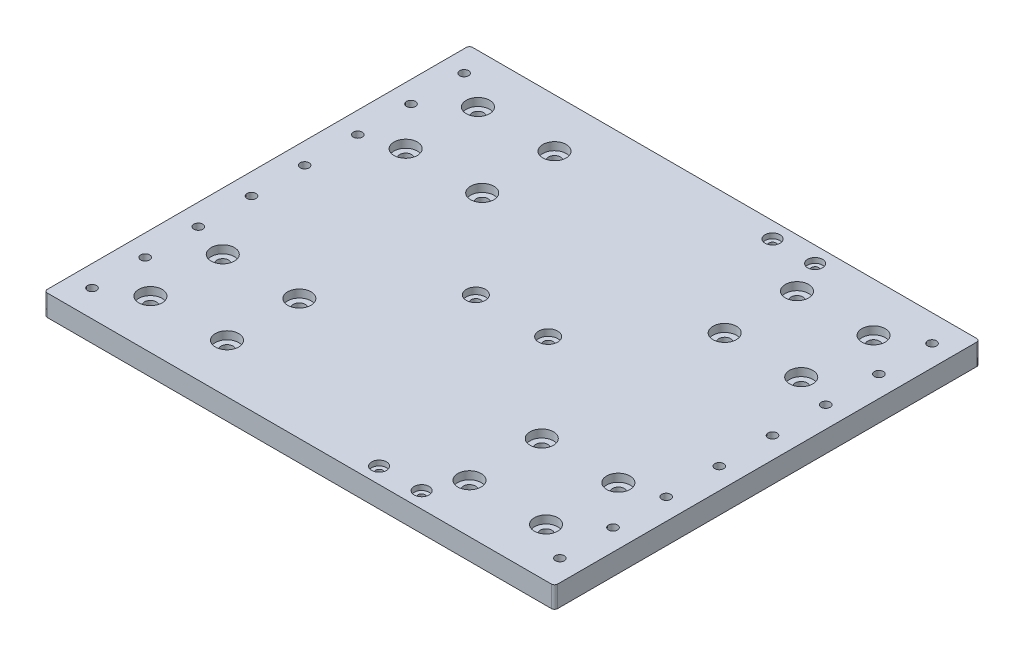
SolidWorks part; units mm, degrees
ref_plane "Front Plane" through (0, 0, 0) normal (0, 0, 1) x (1, 0, 0)
ref_plane "Top Plane" through (0, 0, 0) normal (0, 1, 0) x (1, 0, 0)
ref_plane "Right Plane" through (0, 0, 0) normal (1, 0, 0) x (0, 0, -1)
sketch "Sketch1" plane through (0, 0, 0) normal (0, 1, 0) x (1, 0, 0)
  line L1 (-120, -100) -> (120, -100)
  line L2 (-120, -100) -> (-120, 100)
  line L3 (-120, 100) -> (120, 100)
  line L4 (120, -100) -> (120, 100)
  line L5 (-120, -100) -> (120, 100) construction
  line L6 (-120, 100) -> (120, -100) construction
  point P0 (0, 0)
  dimension "D1" = 240
  dimension "D2" = 200
extrude "Boss-Extrude1" add sketch "Sketch1" along normal mid plane 10
hole_wizard "CBORE for M5 Pan Head Machine Screw1" positions "Sketch11" profile "Sketch10" counterbore size "M5" standard "ANSI Metric" end condition through all
sketch "Sketch11" plane through (66.9231, 5, -81.9693) normal (0, -1, 0) x (-1, 0, 0)
  line L0 (141.9231, -1018.8886) -> (141.9231, 48981.1114) construction
  line L1 (-912.3245, -141.9693) -> (49087.6755, -141.9693) construction
  line L2 (186.9231, 18.0307) -> (186.9231, -181.9693) construction
  line L3 (186.9231, -181.9693) -> (-53.0769, -181.9693) construction
  line L5 (159.9231, -124.9693) -> (123.9231, -124.9693) construction
  line L6 (159.9231, -124.9693) -> (159.9231, -158.9693) construction
  line L7 (159.9231, -158.9693) -> (123.9231, -158.9693) construction
  line L8 (123.9231, -124.9693) -> (123.9231, -158.9693) construction
  line L9 (159.9231, -124.9693) -> (123.9231, -158.9693) construction
  line L10 (159.9231, -158.9693) -> (123.9231, -124.9693) construction
  point P0 (159.9231, -158.9693)
  point P2 (123.9231, -158.9693)
  point P4 (123.9231, -124.9693)
  point P6 (159.9231, -124.9693)
  dimension "D1" = 45
  dimension "D2" = 40
  dimension "D3" = 18
  dimension "D4" = 34
  dimension "D5" = 17
  dimension "D6" = 36
sketch "Sketch10" plane through (-93, 5, 77) normal (1, 0, 0) x (0, 0, 1)
  line L0 (0, 0) -> (0, 10)
  line L1 (0, 10) -> (2.75, 10)
  line L3 (2.75, 10) -> (2.75, 3.7)
  line L4 (2.75, 3.7) -> (5.5, 3.7)
  line L5 (5.5, 3.7) -> (5.5, 0)
  line L7 (5.5, 0) -> (0, 0)
  line L11 (0, -6.35) -> (0, 107.95) construction
  dimension "Thru Hole Dia." = 5.5
  dimension "Thru Hole Depth" = 10
  dimension "C'Bore Dia." = 11
  dimension "C'Bore Depth" = 3.7
mirror "Mirror1" about plane through (0, 0, 0) normal (1, 0, 0) of "CBORE for M5 Pan Head Machine Screw1"
mirror "Mirror2" about plane through (0, 0, 0) normal (0, 0, 1) of "Mirror1", "CBORE for M5 Pan Head Machine Screw1"
hole_wizard "CBORE for M4 Pan Head Machine Screw1" positions "Sketch9" profile "Sketch8" counterbore size "M4" standard "ANSI Metric" end condition through all
sketch "Sketch9" plane through (-30.3385, 5, -23.5385) normal (0, -1, 0) x (-1, 0, 0)
  line L0 (-1000, -23.5385) -> (49000, -23.5385) construction
  point P0 (-13.3385, -23.5385)
  point P2 (-47.3385, -23.5385)
  dimension "D1" = 17
  dimension "D2" = 17
sketch "Sketch8" plane through (-17, 5, 0) normal (1, 0, 0) x (0, 0, 1)
  line L0 (0, 0) -> (0, 10)
  line L1 (0, 10) -> (2.25, 10)
  line L3 (2.25, 10) -> (2.25, 3.1)
  line L4 (2.25, 3.1) -> (4.5, 3.1)
  line L5 (4.5, 3.1) -> (4.5, 0)
  line L7 (4.5, 0) -> (0, 0)
  line L11 (0, -6.35) -> (0, 107.95) construction
  dimension "Thru Hole Dia." = 4.5
  dimension "Thru Hole Depth" = 10
  dimension "C'Bore Dia." = 9
  dimension "C'Bore Depth" = 3.1
hole_wizard "M5x0.8 Tapped Hole1" positions "Sketch7" profile "Sketch5" tap size "M5x0.8" standard "ANSI Metric" end condition through all
sketch "Sketch7" plane through (0, 5, 0) normal (0, 1, 0) x (1, 0, 0)
  line L0 (120, 100) -> (-120, 100) construction
  line L1 (-120, 100) -> (-120, -100) construction
  line L2 (120, -100) -> (120, 100) construction
  point P0 (-110, 87.5)
  point P2 (110, 87.5)
  dimension "D1" = 12.5
  dimension "D2" = 10
  dimension "D3" = 10
  dimension "D4" = 12.5
sketch "Sketch5" plane through (-110, 5, -87.5) normal (1, 0, 0) x (0, 0, 1)
  line L0 (0, 0) -> (0, 10)
  line L1 (0, 10) -> (2.1, 10)
  line L2 (2.1, 10) -> (2.1, 0)
  line L5 (2.1, 0) -> (0, 0)
  line L11 (0, -6.35) -> (0, 107.95) construction
  dimension "Thru Tap Drill Dia." = 4.2
  dimension "Thru Tap Drill Depth" = 10
cosmetic thread "Hole Thread1" parameters "D2"=5
cosmetic thread "Hole Thread2" parameters "D2"=5
fillet "Fillet1" radius 1.5 4 edges at (-120, 0, -100) (120, 0, -100) (-120, 0, 100) (120, 0, 100)
pattern_linear "LPattern2" count 8 spacing 25 along (0, 0, 1) of "M5x0.8 Tapped Hole1"
hole_wizard "CBORE for M3 Pan Head Machine Screw1" positions "Sketch13" profile "Sketch12" counterbore size "M3" standard "ANSI Metric" end condition through all
sketch "Sketch13" plane through (0, 5, 0) normal (0, 1, 0) x (1, 0, 0)
  line L0 (118.5, 100) -> (-118.5, 100) construction
  point P0 (30, 92.5)
  point P2 (50, 92.5)
  dimension "D1" = 50
  dimension "D2" = 20
  dimension "D3" = 7.5
  dimension "D4" = 7.5
sketch "Sketch12" plane through (30, 5, -92.5) normal (1, 0, 0) x (0, 0, 1)
  line L0 (0, 0) -> (0, 10)
  line L1 (0, 10) -> (1.6, 10)
  line L3 (1.6, 10) -> (1.6, 2.4)
  line L4 (1.6, 2.4) -> (3.5, 2.4)
  line L5 (3.5, 2.4) -> (3.5, 0)
  line L7 (3.5, 0) -> (0, 0)
  line L11 (0, -6.35) -> (0, 107.95) construction
  dimension "Thru Hole Dia." = 3.2
  dimension "Thru Hole Depth" = 10
  dimension "C'Bore Dia." = 7
  dimension "C'Bore Depth" = 2.4
mirror "Mirror3" about plane through (0, 0, 0) normal (0, 0, 1) of "CBORE for M3 Pan Head Machine Screw1"
equation "\"D5@Sketch11\"=\"D4@Sketch11\"/2"
equation "\"D3@Sketch11\"=\"D6@Sketch11\"/2"
